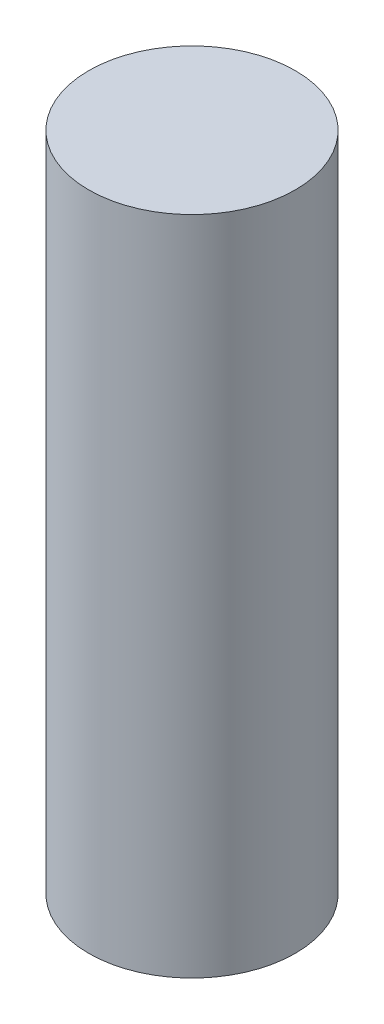
SolidWorks part; units mm, degrees
ref_plane "Front Plane" through (0, 0, 0) normal (0, 0, 1) x (1, 0, 0)
ref_plane "Top Plane" through (0, 0, 0) normal (0, 1, 0) x (1, 0, 0)
ref_plane "Right Plane" through (0, 0, 0) normal (1, 0, 0) x (0, 0, -1)
sketch "Sketch1" plane through (0, 0, 0) normal (0, 1, 0) x (1, 0, 0)
  circle A0 centre (0, 0) radius 9.525
  dimension "D1" = 19.05
extrude "Boss-Extrude1" add sketch "Sketch1" along normal blind 60.96
